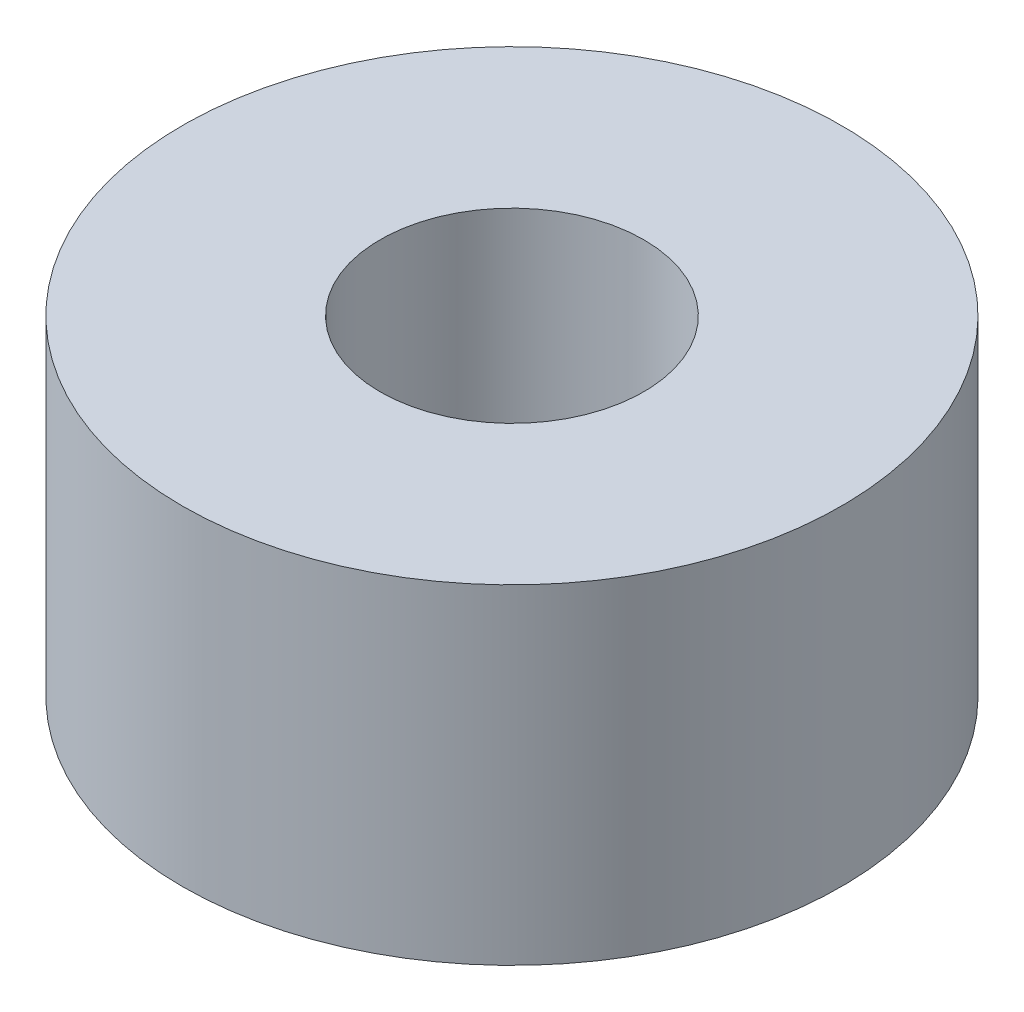
SolidWorks part; units mm, degrees
ref_plane "Спереди" through (0, 0, 0) normal (0, 0, 1) x (1, 0, 0)
ref_plane "Сверху" through (0, 0, 0) normal (0, 1, 0) x (1, 0, 0)
ref_plane "Справа" through (0, 0, 0) normal (1, 0, 0) x (0, 0, -1)
sketch "Эскиз1" plane through (0, 0, 0) normal (0, 1, 0) x (1, 0, 0)
  circle A0 centre (0, 0) radius 2.5
  circle A1 centre (0, 0) radius 1
extrude "Бобышка-Вытянуть1" add sketch "Эскиз1" along normal blind 2.5
